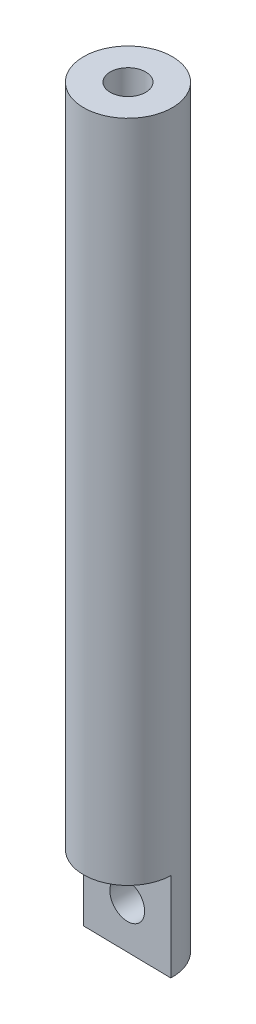
SolidWorks part; units mm, degrees
ref_plane "Front Plane" through (0, 0, 0) normal (0, 0, 1) x (1, 0, 0)
ref_plane "Top Plane" through (0, 0, 0) normal (0, 1, 0) x (1, 0, 0)
ref_plane "Right Plane" through (0, 0, 0) normal (1, 0, 0) x (0, 0, -1)
sketch "Sketch1" plane through (0, 0, 0) normal (0, 1, 0) x (1, 0, 0)
  circle A0 centre (0, 0) radius 5
extrude "Boss-Extrude1" add sketch "Sketch1" along normal blind 85
sketch "Sketch2" plane through (0, 85, 0) normal (0, 1, 0) x (1, 0, 0)
  circle A0 centre (0, 0) radius 2
extrude "Cut-Extrude1" cut sketch "Sketch2" against normal blind 15
sketch "Sketch3" plane through (0, 0, 0) normal (0, -1, 0) x (1, 0, 0)
  line L0 (-5, 0) -> (4.9972, 0.1666)
  circle A1 centre (0, 0) radius 5 construction
  arc A2 (-5, 0) -> (4.9972, 0.1666) centre (-0.0014, 0.0833) cw
extrude "Cut-Extrude2" cut sketch "Sketch3" against normal blind 10
sketch "Sketch4" plane through (-0.0014, 0, 0.0833) normal (-0.0167, 0, 0.9999) x (0.9999, 0, 0.0167)
  circle A0 centre (0, 5) radius 2
extrude "Cut-Extrude3" cut sketch "Sketch4" against normal through all
